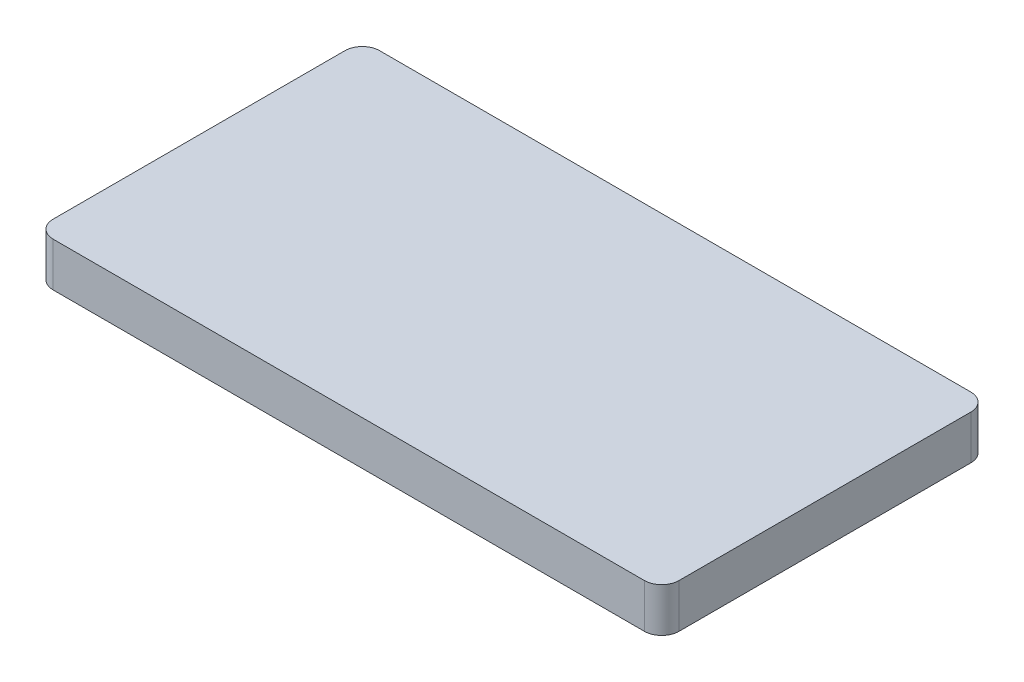
SolidWorks part; units mm, degrees
material "1023 Carbon Steel Sheet (SS)"
ref_plane "Front Plane" through (0, 0, 0) normal (0, 0, 1) x (1, 0, 0)
ref_plane "Top Plane" through (0, 0, 0) normal (0, 1, 0) x (1, 0, 0)
ref_plane "Right Plane" through (0, 0, 0) normal (1, 0, 0) x (0, 0, -1)
sketch "Sketch1" plane through (0, 0, 0) normal (0, 1, 0) x (1, 0, 0)
  line L1 (-45.15, 23.55) -> (45.15, 23.55)
  line L2 (-45.15, 23.55) -> (-45.15, -23.55)
  line L3 (-45.15, -23.55) -> (45.15, -23.55)
  line L4 (45.15, 23.55) -> (45.15, -23.55)
  point P4 (0, 23.55)
  point P5 (45.15, 0)
  dimension "D1" = 47.1
  dimension "D2" = 90.3
extrude "Boss-Extrude1" add sketch "Sketch1" along normal blind 6.35
fillet "Fillet1" radius 2.5 4 edges at (-45.15, 3.175, -23.55) (-45.15, 3.175, 23.55) (45.15, 3.175, -23.55) (45.15, 3.175, 23.55)
